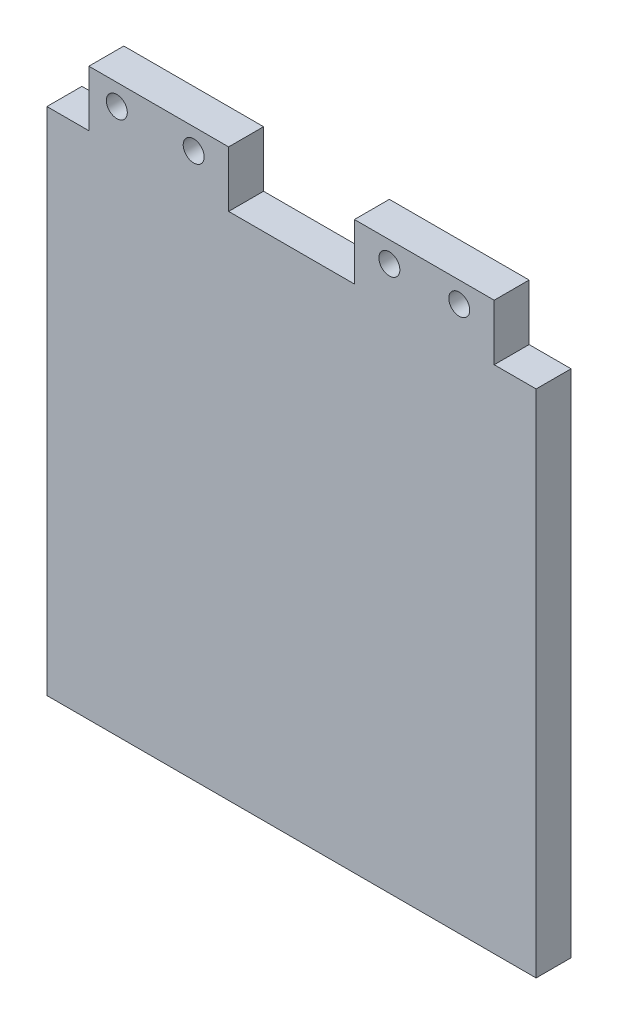
SolidWorks part; units mm, degrees
ref_plane "Plano frontal" through (0, 0, 0) normal (0, 0, 1) x (1, 0, 0)
ref_plane "Plano superior" through (0, 0, 0) normal (0, 1, 0) x (1, 0, 0)
ref_plane "Plano direito" through (0, 0, 0) normal (1, 0, 0) x (0, 0, -1)
sketch "Esboço1" plane through (0, 0, 0) normal (0, 0, 1) x (1, 0, 0)
  line L0 (-1.557, 38.1429) -> (16.443, 38.1429)
  line L1 (-27.557, -34.8571) -> (42.443, -34.8571)
  line L2 (-27.557, -34.8571) -> (-27.557, 38.1429)
  line L3 (-27.557, 38.1429) -> (-21.557, 38.1429)
  line L4 (42.443, -34.8571) -> (42.443, 38.1429)
  line L5 (36.443, 38.1429) -> (42.443, 38.1429)
  line L6 (-21.557, 38.1429) -> (-21.557, 46.1429)
  line L7 (-21.557, 46.1429) -> (-1.557, 46.1429)
  line L8 (-1.557, 38.1429) -> (-1.557, 46.1429)
  line L10 (16.443, 38.1429) -> (16.443, 46.1429)
  line L11 (16.443, 46.1429) -> (36.443, 46.1429)
  line L12 (36.443, 38.1429) -> (36.443, 46.1429)
  dimension "D1" = 70
  dimension "D2" = 20
  dimension "D3" = 8
  dimension "D4" = 6
  dimension "D5" = 18
  dimension "D6" = 20
  dimension "D7" = 8
  dimension "D8" = 73
extrude "Ressalto-extrusão1" add sketch "Esboço1" along normal blind 5 contours L0 L10 L11 L12 L5 L4 L1 L2 L3 L6 L7 L8
sketch "Esboço2" plane through (0, 0, 5) normal (0, 0, 1) x (1, 0, 0)
  line L1 (-21.557, 46.1429) -> (-1.557, 46.1429) construction
  line L2 (-21.557, 38.1429) -> (-21.557, 46.1429) construction
  circle A0 centre (-17.557, 43.1429) radius 1.5
  circle A1 centre (-6.557, 43.1429) radius 1.5
  dimension "D1" = 4
  dimension "D2" = 3
  dimension "D3" = 11
  dimension "D4" = 3
  dimension "D5" = 3
  dimension "D6" = 3
extrude "Corte-extrusão1" cut sketch "Esboço2" against normal blind 10
sketch "Esboço3" plane through (0, 0, 5) normal (0, 0, 1) x (1, 0, 0)
  line L1 (16.443, 38.1429) -> (16.443, 46.1429) construction
  line L3 (16.443, 46.1429) -> (36.443, 46.1429) construction
  line L4 (36.443, 38.1429) -> (36.443, 46.1429) construction
  circle A0 centre (21.443, 43.1429) radius 1.5
  circle A1 centre (31.443, 43.1429) radius 1.5
  point P6 (16.443, 42.1429)
  dimension "D1" = 3
  dimension "D2" = 3
  dimension "D3" = 5
  dimension "D4" = 3
  dimension "D5" = 5
extrude "Corte-extrusão2" cut sketch "Esboço3" against normal through all
